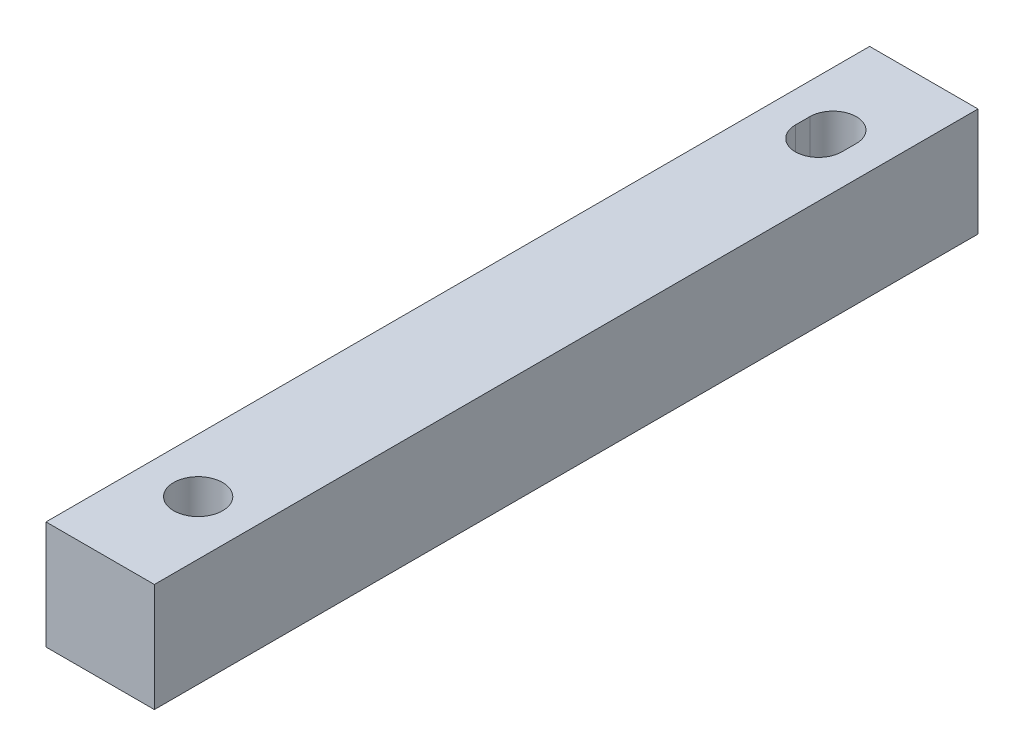
SolidWorks part; units mm, degrees
ref_plane "Front Plane" through (0, 0, 0) normal (0, 0, 1) x (1, 0, 0)
ref_plane "Top Plane" through (0, 0, 0) normal (0, 1, 0) x (1, 0, 0)
ref_plane "Right Plane" through (0, 0, 0) normal (1, 0, 0) x (0, 0, -1)
sketch "Sketch1" plane through (0, 0, 0) normal (0, 1, 0) x (1, 0, 0)
  line L1 (-25.7386, -52.5568) -> (-16.2136, -52.5568)
  line L2 (-25.7386, -52.5568) -> (-25.7386, 19.8332)
  line L3 (-25.7386, 19.8332) -> (-16.2136, 19.8332)
  line L4 (-16.2136, -52.5568) -> (-16.2136, 19.8332)
  dimension "D1" = 72.39
  dimension "D2" = 9.525
extrude "Boss-Extrude1" add sketch "Sketch1" along normal blind 9.525
sketch "Sketch4" plane through (0, 9.525, 0) normal (0, 1, 0) x (1, 0, 0)
  line L0 (-20.9761, 11.8561) -> (-20.9761, 10.5861) construction
  line L1 (-18.9307, 11.8561) -> (-18.9307, 10.5861)
  line L2 (-23.0215, 11.8561) -> (-23.0215, 10.5861)
  line L4 (-25.7386, 19.8332) -> (-25.7386, -52.5568) construction
  line L5 (-16.2136, 19.8332) -> (-25.7386, 19.8332) construction
  arc A0 (-18.9307, 11.8561) -> (-23.0215, 11.8561) centre (-20.9761, 11.8561) ccw
  arc A1 (-23.0215, 10.5861) -> (-18.9307, 10.5861) centre (-20.9761, 10.5861) ccw
  point P2 (-20.9761, 11.2211)
  dimension "D1" = 4.0908
  dimension "D2" = 1.27
  dimension "D3" = 4.7625
  dimension "D4" = 8.6122
hole_wizard "#18 (0.1695) Diameter Hole1" positions "Sketch6" profile "Sketch5" hole size "#18" standard "Ansi Inch"
sketch "Sketch6" plane through (0, 9.525, 0) normal (0, 1, 0) x (-1, 0, 0)
  line L1 (16.2136, 52.5568) -> (16.2136, -19.8332) construction
  point P0 (20.9761, 43.9446)
  dimension "D1" = 55.1656
  dimension "D2" = 4.7625
sketch "Sketch5" plane through (-20.9761, 9.525, 43.9446) normal (1, 0, 0) x (0, 0, 1)
  line L0 (0, 0) -> (0, 16.5334)
  line L1 (0, 16.5334) -> (2.1526, 15.24)
  line L2 (2.1526, 15.24) -> (2.1526, 0)
  line L5 (2.1526, 0) -> (0, 0)
  line L10 (0, 16.5334) -> (-2.1527, 15.24) construction
  line L11 (0, -6.35) -> (0, 107.95) construction
  dimension "Hole Dia." = 4.3053
  dimension "Hole Depth" = 15.24
  dimension "Drill Angle" = 118
extrude "Cut-Extrude1" cut sketch "Sketch4" against normal up to next
equation "\"D3@Sketch4\" = \"D2@Sketch1\"/2"
equation "\"D2@Sketch6\" = \"D2@Sketch1\"/2"
